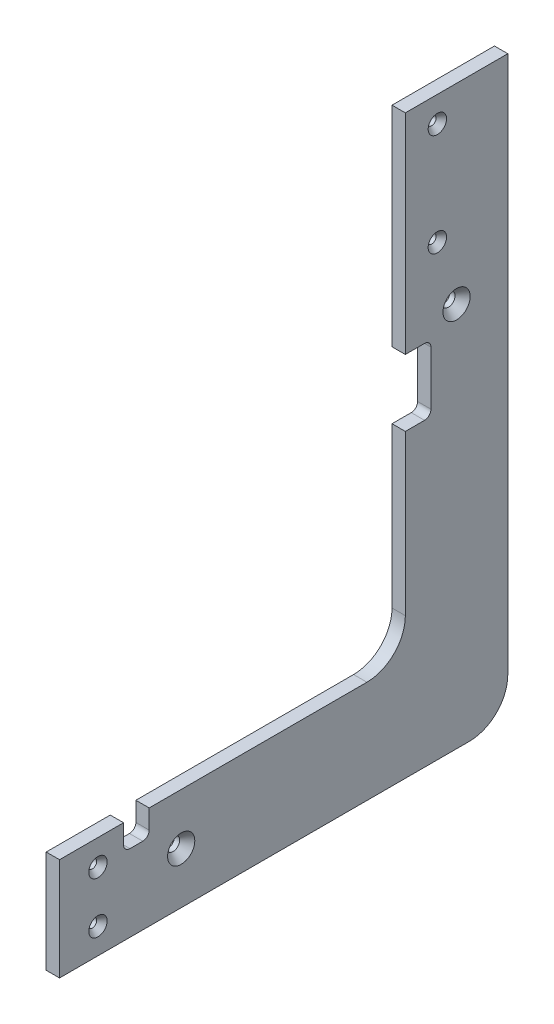
SolidWorks part; units mm, degrees
material "Acrylic (BLUE)"
ref_plane "Front Plane" through (0, 0, 0) normal (0, 0, 1) x (1, 0, 0)
ref_plane "Top Plane" through (0, 0, 0) normal (0, 1, 0) x (1, 0, 0)
ref_plane "Right Plane" through (0, 0, 0) normal (1, 0, 0) x (0, 0, -1)
sketch "Sketch1" plane through (0, 0, 0) normal (1, 0, 0) x (0, 0, -1)
  line L0 (-222.25, 0) -> (-171.45, 0)
  line L1 (-165.1, 0) -> (165.1, 0) construction
  line L2 (-165.1, 0) -> (-165.1, -228.6) construction
  line L3 (-165.1, -228.6) -> (165.1, -228.6) construction
  line L4 (165.1, 0) -> (165.1, -228.6) construction
  line L5 (171.45, 0) -> (222.25, 0)
  line L6 (-171.45, 0) -> (-171.45, -215.9)
  line L7 (-152.4, -234.95) -> (152.4, -234.95)
  line L8 (171.45, 0) -> (171.45, -215.9)
  line L9 (-165.1, 0) -> (-165.1, 25.4) construction
  line L10 (-222.25, 0) -> (-222.25, -266.7)
  line L11 (-203.2, -285.75) -> (203.2, -285.75)
  line L12 (222.25, 0) -> (222.25, -266.7)
  line L13 (-165.1, 25.4) -> (165.1, 25.4) construction
  line L14 (165.1, 25.4) -> (165.1, 0) construction
  line L15 (0, -234.95) -> (0, -285.75)
  arc A0 (203.2, -285.75) -> (222.25, -266.7) centre (203.2, -266.7) ccw
  arc A1 (-203.2, -285.75) -> (-222.25, -266.7) centre (-203.2, -266.7) cw
  arc A2 (171.45, -215.9) -> (152.4, -234.95) centre (152.4, -215.9) cw
  arc A3 (-152.4, -234.95) -> (-171.45, -215.9) centre (-152.4, -215.9) cw
  dimension "D8" = 19.05
  dimension "D1" = 50.8
  dimension "D2" = 330.2
  dimension "D3" = 228.6
  dimension "D4" = 6.35
  dimension "D5" = 6.35
  dimension "D6" = 6.35
  dimension "D7" = 50.8
  dimension "D9" = 254
  dimension "D10" = 25.4
  dimension "D11" = 285.75
extrude "Boss-Extrude2" add sketch "Sketch1" along normal blind 6.604 contours L8 A2 L7 L15 L11 A0 L12 L5
hole_wizard "CSK for #8 Flat Head Socket Cap Screw1" positions "Sketch4" profile "Sketch5" countersink size "#8" standard "ANSI Inch" end condition through all
sketch "Sketch4" plane through (6.604, -103.9714, -28.9631) normal (-1, 0, 0) x (0, 0, 1)
  line L15 (-158.3619, 91.2714) -> (-158.3619, 40.4714) construction
  line L16 (-158.3619, 40.4714) -> (-158.3619, 27.7714) construction
  line L18 (-158.3619, 91.2714) -> (-158.3619, 103.9714) construction
  line L20 (-142.4869, 103.9714) -> (-142.4869, -111.9286) construction
  line L21 (-142.4869, 103.9714) -> (-193.2869, 103.9714) construction
  point P37 (-158.3619, 91.2714)
  point P39 (-158.3619, 40.4714)
  dimension "D1" = 15.875
  dimension "D2" = 76.2
  dimension "D3" = 12.7
sketch "Sketch5" plane through (6.604, -12.7, -187.325) normal (0, 1, 0) x (0, 0, -1)
  line L0 (0, 0) -> (0, 6.604)
  line L1 (0, 6.604) -> (2.1526, 6.604)
  line L2 (2.1526, 6.604) -> (2.1526, 2.7685)
  line L3 (2.1526, 2.7685) -> (4.5593, 0)
  line L5 (4.5593, 0) -> (0, 0)
  line L6 (-2.1526, 2.7685) -> (-4.5593, 0) construction
  line L11 (0, -6.35) -> (0, 107.95) construction
  dimension "Thru Hole Dia." = 4.3053
  dimension "Thru Hole Depth" = 6.604
  dimension "Near C'Sink Dia." = 9.1186
  dimension "Near C'Sink Angle" = 82
hole_wizard "CSK for #8 Flat Head Socket Cap Screw2" positions "Sketch8" profile "Sketch7" countersink size "#8" standard "ANSI Inch" end condition through all
sketch "Sketch8" plane through (6.604, 143.8224, -169.2827) normal (-1, 0, 0) x (0, 0, 1)
  line L1 (150.2327, -378.7724) -> (150.2327, -391.4724) construction
  line L2 (169.2827, -378.7724) -> (16.8827, -378.7724) construction
  line L3 (150.2327, -391.4724) -> (150.2327, -416.8724) construction
  line L4 (150.2327, -416.8724) -> (150.2327, -429.5724) construction
  line L5 (169.2827, -429.5724) -> (-33.9173, -429.5724) construction
  line L6 (169.2827, -378.7724) -> (169.2827, -429.5724) construction
  point P3 (150.2327, -391.4724)
  point P7 (150.2327, -416.8724)
  dimension "D1" = 12.7
  dimension "D2" = 19.05
sketch "Sketch7" plane through (6.604, -247.65, -19.05) normal (0, 1, 0) x (0, 0, -1)
  line L0 (0, 0) -> (0, 6.604)
  line L1 (0, 6.604) -> (2.1526, 6.604)
  line L2 (2.1526, 6.604) -> (2.1526, 2.7685)
  line L3 (2.1526, 2.7685) -> (4.5593, 0)
  line L5 (4.5593, 0) -> (0, 0)
  line L6 (-2.1526, 2.7685) -> (-4.5593, 0) construction
  line L11 (0, -6.35) -> (0, 107.95) construction
  dimension "Thru Hole Dia." = 4.3053
  dimension "Thru Hole Depth" = 6.604
  dimension "Near C'Sink Dia." = 9.1186
  dimension "Near C'Sink Angle" = 82
hole_wizard "CSK for 1/4 Flat Head Socket Cap Screw1" positions "Sketch10" profile "Sketch9" countersink size "1/4" standard "ANSI Inch" end condition through all
sketch "Sketch10" plane through (6.604, 0, 0) normal (1, 0, 0) x (0, 0, -1)
  line L0 (196.85, 0) -> (196.85, -94.869) construction
  line L1 (171.45, 0) -> (222.25, 0) construction
  line L2 (0, -260.35) -> (60.325, -260.35) construction
  line L3 (0, -234.95) -> (0, -285.75) construction
  point P1 (196.85, -94.869)
  point P4 (60.325, -260.35)
  dimension "D1" = 94.869
  dimension "D2" = 60.325
sketch "Sketch9" plane through (6.604, -94.869, -196.85) normal (0, 1, 0) x (0, 0, -1)
  line L0 (0, 0) -> (0, 6.604)
  line L1 (0, 6.604) -> (3.2639, 6.604)
  line L2 (3.2639, 6.604) -> (3.2639, 4.0031)
  line L3 (3.2639, 4.0031) -> (6.7437, 0)
  line L5 (6.7437, 0) -> (0, 0)
  line L6 (-3.2639, 4.0031) -> (-6.7437, 0) construction
  line L11 (0, -6.35) -> (0, 107.95) construction
  dimension "Thru Hole Dia." = 6.5278
  dimension "Thru Hole Depth" = 6.604
  dimension "Near C'Sink Dia." = 13.4874
  dimension "Near C'Sink Angle" = 82
sketch "Sketch11" plane through (0, 0, 0) normal (-1, 0, 0) x (0, 0, 1)
  line L0 (-171.45, 0) -> (-171.45, -215.9) construction
  line L1 (-171.45, -103.759) -> (-180.975, -103.759)
  line L2 (-171.45, -103.759) -> (-171.45, -136.779)
  line L3 (-171.45, -136.779) -> (-180.975, -136.779)
  line L4 (-184.15, -106.934) -> (-184.15, -133.604)
  line L6 (-171.45, -120.269) -> (-171.45, 0) construction
  line L7 (0, -234.95) -> (-152.4, -234.95) construction
  line L8 (-44.45, -234.95) -> (-31.75, -234.95)
  line L9 (-44.45, -234.95) -> (-44.45, -244.475)
  line L10 (-41.275, -247.65) -> (-34.925, -247.65)
  line L11 (-31.75, -234.95) -> (-31.75, -244.475)
  line L13 (-38.1, -234.95) -> (0, -234.95) construction
  line L14 (0, -234.95) -> (0, -285.75) construction
  arc A0 (-180.975, -136.779) -> (-184.15, -133.604) centre (-180.975, -133.604) cw
  arc A1 (-184.15, -106.934) -> (-180.975, -103.759) centre (-180.975, -106.934) cw
  arc A2 (-34.925, -247.65) -> (-31.75, -244.475) centre (-34.925, -244.475) ccw
  arc A3 (-41.275, -247.65) -> (-44.45, -244.475) centre (-41.275, -244.475) cw
  point P10 (-184.15, -136.779)
  point P13 (-184.15, -103.759)
  point P25 (-31.75, -247.65)
  point P28 (-44.45, -247.65)
  dimension "D4" = 3.175
  dimension "D8" = 3.175
  dimension "D1" = 12.7
  dimension "D2" = 33.02
  dimension "D3" = 120.269
  dimension "D5" = 12.7
  dimension "D6" = 12.7
  dimension "D7" = 38.1
extrude "Cut-Extrude1" cut sketch "Sketch11" against normal through all
other "Move Face1" [suppressed] parameters "D1"=0.0508
